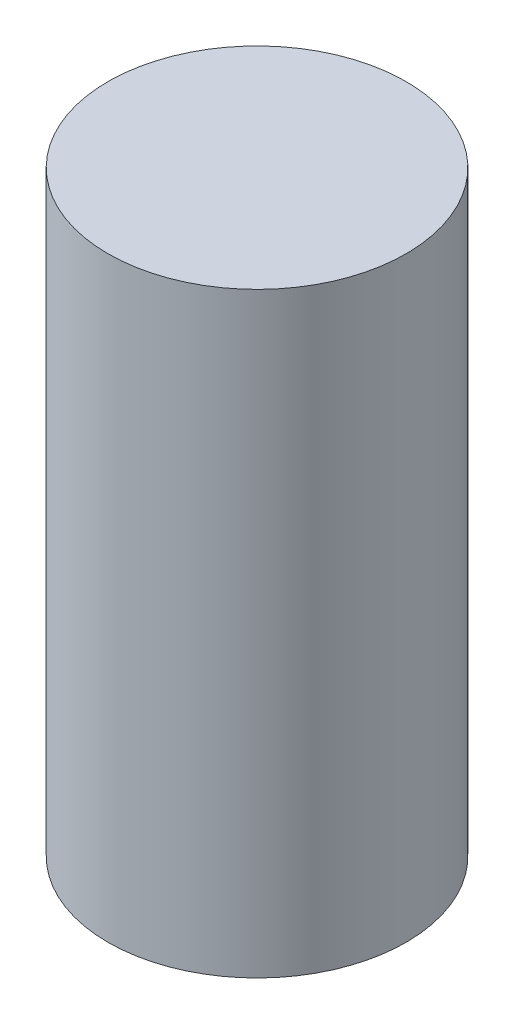
SolidWorks part; units mm, degrees
ref_plane "Front Plane" through (0, 0, 0) normal (0, 0, 1) x (1, 0, 0)
ref_plane "Top Plane" through (0, 0, 0) normal (0, 1, 0) x (1, 0, 0)
ref_plane "Right Plane" through (0, 0, 0) normal (1, 0, 0) x (0, 0, -1)
sketch "Sketch1" plane through (0, 0, 0) normal (0, 1, 0) x (1, 0, 0)
  circle A0 centre (0, 0) radius 0.7937
  dimension "D1" = 1.5875
extrude "Boss-Extrude1" add sketch "Sketch1" along normal blind 3.175
